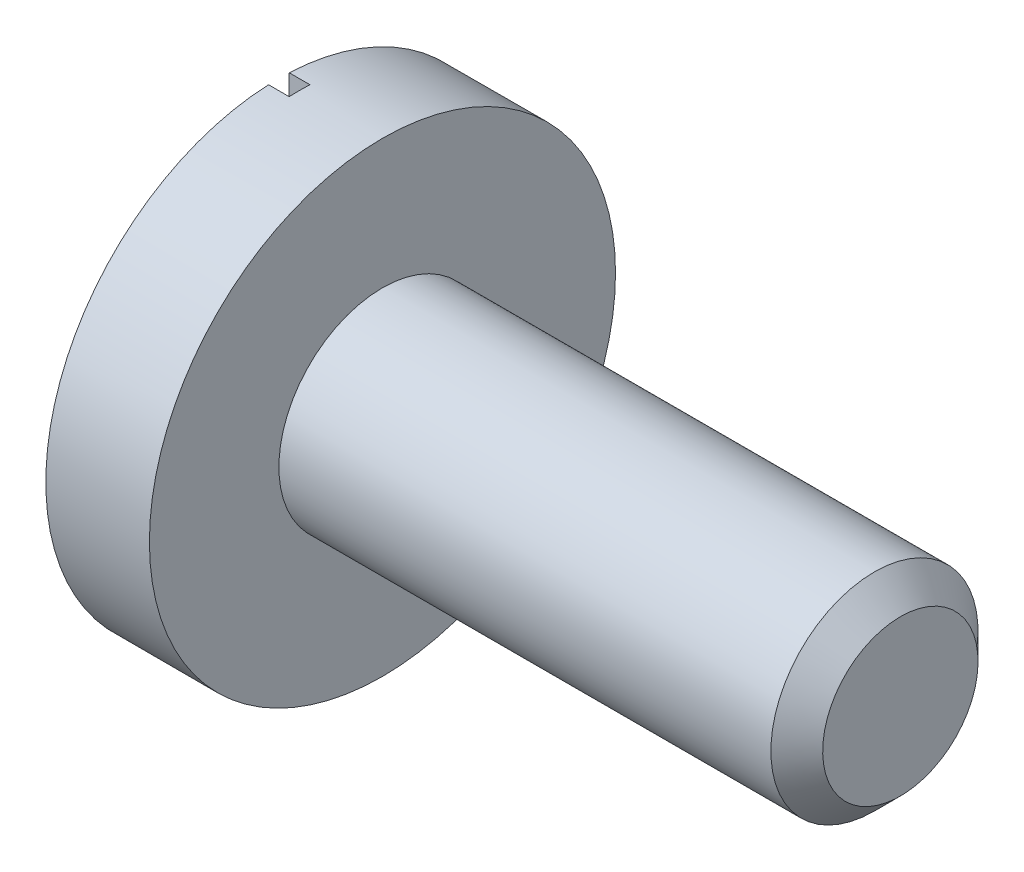
SolidWorks part; units mm, degrees
ref_plane "Front Plane" through (0, 0, 0) normal (0, 0, 1) x (1, 0, 0)
ref_plane "Top Plane" through (0, 0, 0) normal (0, 1, 0) x (1, 0, 0)
ref_plane "Right Plane" through (0, 0, 0) normal (1, 0, 0) x (0, 0, -1)
sketch "Croquis1" plane through (0, 0, 0) normal (0, 0, 1) x (1, 0, 0)
  line L0 (0, 0) -> (0, 1.125)
  line L1 (0, 1.125) -> (0.5, 1.125)
  line L2 (0.5, 1.125) -> (0.5, 0.5)
  line L3 (0.5, 0.5) -> (3, 0.5)
  line L4 (3, 0) -> (3, 0.5)
  line L7 (3, 0) -> (0, 0)
  dimension "D2" = 1.125
  dimension "D4" = 0.5
  dimension "D6" = 0.5
  dimension "D7" = 3
revolve "Revolución1" add sketch "Croquis1" angle 360 about L7
cosmetic thread "Rosca cosmética1" parameters "D2"=0.75
chamfer "Chaflán1" distance 0.125 angle 45 1 edges at (3, 0.5, 0)
sketch "Croquis6" plane through (0, 0, 0) normal (-1, 0, 0) x (0, 0, 1)
  line L2 (-0.05, 1.1239) -> (-0.05, -1.1239)
  line L4 (0.05, 1.1239) -> (0.05, -1.1239)
  arc A0 (-0.05, -1.1239) -> (0.05, -1.1239) centre (0, 0) ccw
  circle A1 centre (0, 0) radius 1.125 construction
  arc A2 (0.05, 1.1239) -> (-0.05, 1.1239) centre (0, 0) ccw
  dimension "D1" = 0.1
extrude "Cortar-Extruir2" cut sketch "Croquis6" against normal blind 0.1
